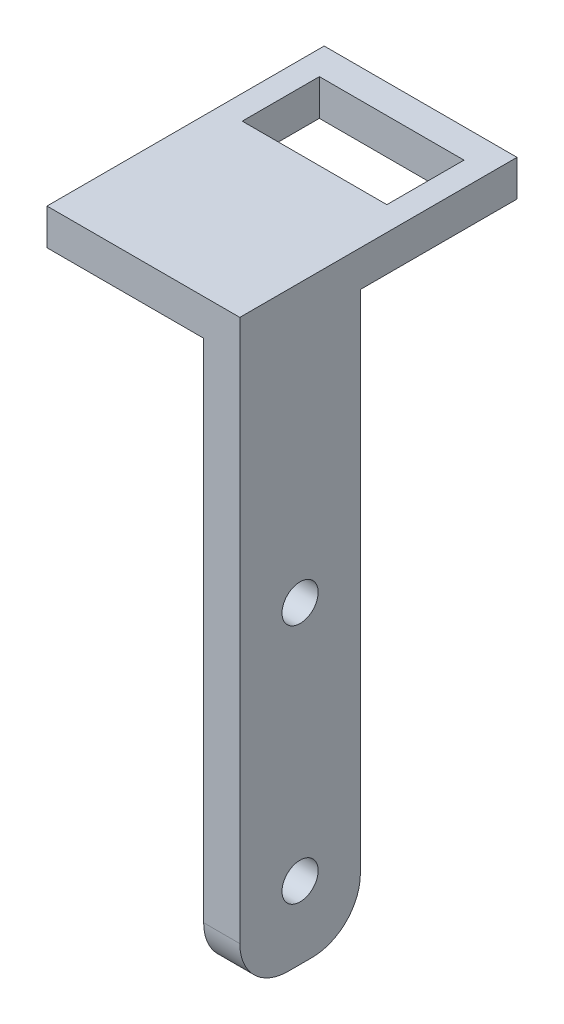
SolidWorks part; units mm, degrees
material "Plain Carbon Steel"
ref_plane "Front Plane" through (0, 0, 0) normal (0, 0, 1) x (1, 0, 0)
ref_plane "Top Plane" through (0, 0, 0) normal (0, 1, 0) x (1, 0, 0)
ref_plane "Right Plane" through (0, 0, 0) normal (1, 0, 0) x (0, 0, -1)
sketch "Sketch1" plane through (0, 0, 0) normal (1, 0, 0) x (0, 0, -1)
  line L1 (-7.9375, 25.4) -> (7.9375, 25.4)
  line L2 (-7.9375, 25.4) -> (-7.9375, -25.4)
  line L3 (-7.9375, -25.4) -> (7.9375, -25.4)
  line L4 (7.9375, 25.4) -> (7.9375, -25.4)
  line L5 (-7.9375, 25.4) -> (7.9375, 25.4)
  line L6 (-7.9375, 25.4) -> (-7.9375, 47.625)
  line L7 (-7.9375, 47.625) -> (7.9375, 47.625)
  line L8 (7.9375, 25.4) -> (7.9375, 47.625)
  dimension "D3" = 50.8
  dimension "D1" = 15.875
  dimension "D2" = 7.9375
  dimension "D4" = 25.4
  dimension "D5" = 22.225
extrude "Boss-Extrude1" add sketch "Sketch1" along normal blind 4.7625 contours L1 L8 L7 L6 | L4 L1 L2 L3
hole_wizard "3/16 (0.1875) Diameter Hole1" positions "Sketch3" profile "Sketch4" hole size "3/16" standard "ANSI Inch" end condition through all
sketch "Sketch3" plane through (4.7625, 0, 0) normal (1, 0, 0) x (0, 0, -1)
  line L0 (7.9375, 25.4) -> (-7.9375, 25.4)
  line L1 (7.9375, -25.4) -> (7.9375, 47.625) construction
  line L2 (-7.9375, -25.4) -> (-7.9375, 47.625) construction
  line L4 (-7.9375, -25.4) -> (7.9375, -25.4) construction
  point P0 (0, -15.875)
  point P2 (0, 15.875)
  dimension "D1" = 31.75
  dimension "D2" = 50.8
  dimension "D3" = 9.525
sketch "Sketch4" plane through (4.7625, -15.875, 0) normal (0, 1, 0) x (0, 0, -1)
  line L0 (0, 0) -> (0, 4.7625)
  line L1 (0, 4.7625) -> (2.3812, 4.7625)
  line L2 (2.3812, 4.7625) -> (2.3812, 0)
  line L5 (2.3812, 0) -> (0, 0)
  line L11 (0, -6.35) -> (0, 107.95) construction
  dimension "Thru Hole Dia." = 4.7625
  dimension "Thru Hole Depth" = 4.7625
sketch "Sketch5" plane through (0, 47.625, 0) normal (0, 1, 0) x (1, 0, 0)
  line L1 (4.7625, -7.9375) -> (-20.6375, -7.9375)
  line L2 (4.7625, -7.9375) -> (4.7625, 28.575)
  line L3 (4.7625, 28.575) -> (-20.6375, 28.575)
  line L4 (0, 7.9375) -> (0, -7.9375)
  line L5 (0, -7.9375) -> (4.7625, -7.9375)
  line L6 (4.7625, -7.9375) -> (4.7625, 7.9375)
  line L7 (4.7625, 7.9375) -> (0, 7.9375)
  line L8 (0, 7.9375) -> (0, -7.9375)
  line L9 (0, -7.9375) -> (4.7625, -7.9375)
  line L10 (4.7625, -7.9375) -> (4.7625, 7.9375)
  line L11 (4.7625, 7.9375) -> (0, 7.9375)
  line L12 (-20.6375, -7.9375) -> (-20.6375, 28.575)
  line M5 (0, 7.9375) -> (0, -7.9375)
  line M6 (0, -7.9375) -> (4.7625, -7.9375)
  line M7 (4.7625, -7.9375) -> (4.7625, 7.9375)
  line M8 (4.7625, 7.9375) -> (0, 7.9375)
  dimension "D2" = 36.5125
  dimension "D3" = 25.4
  dimension "D1" = 0
extrude "Boss-Extrude2" add sketch "Sketch5" along normal blind 4.7625 contours L12 L1 L2 L3 M5 M8 | M8 M5 M6 M7
fillet "Fillet1" radius 6.35 2 edges at (2.3813, -25.4, 7.9375) (2.3813, -25.4, -7.9375)
sketch "Sketch7" plane through (0, 52.3875, 0) normal (0, 1, 0) x (1, 0, 0)
  line L1 (-17.4625, 14.605) -> (1.5875, 14.605)
  line L2 (-17.4625, 14.605) -> (-17.4625, 24.765)
  line L3 (-17.4625, 24.765) -> (1.5875, 24.765)
  line L4 (1.5875, 14.605) -> (1.5875, 24.765)
  line L5 (-20.6375, -7.9375) -> (-20.6375, 28.575) construction
  line L6 (4.7625, 28.575) -> (-20.6375, 28.575) construction
  dimension "D1" = 10.16
  dimension "D2" = 19.05
  dimension "D3" = 3.175
  dimension "D4" = 13.97
extrude "Cut-Extrude1" cut sketch "Sketch7" against normal through all
equation "\"D2@Sketch1\"=\"D1@Sketch1\"/2"
equation "\"D4@Sketch1\"=\"D3@Sketch1\"/2"
equation "\"D3@Sketch3\"=(\"D2@Sketch3\"-\"D1@Sketch3\")/2"
equation "\"D2@Sketch5\"=.625+13/16"
equation "\"D4@Sketch7\"=.75 - (\"D1@Sketch7\"/2)"
